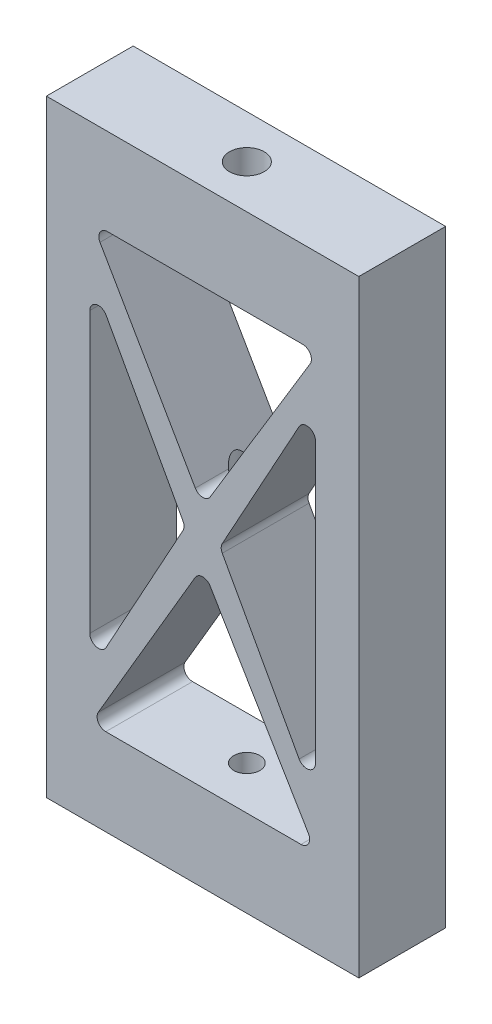
SolidWorks part; units mm, degrees
ref_plane "Ebene vorne" through (0, 0, 0) normal (0, 0, 1) x (1, 0, 0)
ref_plane "Ebene oben" through (0, 0, 0) normal (0, 1, 0) x (1, 0, 0)
ref_plane "Ebene rechts" through (0, 0, 0) normal (1, 0, 0) x (0, 0, -1)
sketch "Skizze1" plane through (0, 0, 0) normal (0, 0, 1) x (1, 0, 0)
  line L0 (-13.0958, 70) -> (22.9042, 70)
  line L5 (-13.0958, 0) -> (22.9042, 0)
  line L6 (-13.0958, 70) -> (-13.0958, 0)
  line L7 (22.9042, 70) -> (22.9042, 0)
  line L10 (17.9042, 51.1068) -> (17.9042, 18.8932)
  line L11 (-8.0958, 51.1068) -> (-8.0958, 18.8932)
  line L12 (16.028, 51.5887) -> (7.1693, 35.4819)
  line L13 (7.1693, 34.5181) -> (16.028, 18.4113)
  line L14 (-6.2196, 51.5887) -> (2.6392, 35.4819)
  line L15 (2.6392, 34.5181) -> (-6.2196, 18.4113)
  line L16 (-6.0537, 60) -> (16.4413, 60)
  line L17 (17.2969, 58.4823) -> (5.7804, 39.4481)
  line L18 (4.0586, 39.4662) -> (-6.9199, 58.5004)
  line L19 (-6.2541, 10) -> (16.241, 10)
  line L20 (17.1003, 11.5115) -> (5.7699, 30.5458)
  line L21 (4.048, 30.5403) -> (-7.1167, 11.5059)
  arc A0 (17.9042, 51.1068) -> (16.028, 51.5887) centre (16.9042, 51.1068) ccw
  arc A1 (17.9042, 18.8932) -> (16.028, 18.4113) centre (16.9042, 18.8932) cw
  arc A2 (7.1693, 35.4819) -> (7.1693, 34.5181) centre (8.0455, 35) ccw
  arc A3 (5.7804, 39.4481) -> (4.0586, 39.4662) centre (4.9248, 39.9658) cw
  arc A4 (16.4413, 60) -> (17.2969, 58.4823) centre (16.4413, 59) cw
  arc A5 (-6.0537, 60) -> (-6.9199, 58.5004) centre (-6.0537, 59) ccw
  arc A6 (-8.0958, 51.1068) -> (-6.2196, 51.5887) centre (-7.0958, 51.1068) cw
  arc A7 (-8.0958, 18.8932) -> (-6.2196, 18.4113) centre (-7.0958, 18.8932) ccw
  arc A8 (2.6392, 35.4819) -> (2.6392, 34.5181) centre (1.763, 35) cw
  arc A9 (5.7699, 30.5458) -> (4.048, 30.5403) centre (4.9106, 30.0343) ccw
  arc A10 (16.241, 10) -> (17.1003, 11.5115) centre (16.241, 11) ccw
  arc A11 (-6.2541, 10) -> (-7.1167, 11.5059) centre (-6.2541, 11) cw
  point P8 (4.9042, 41.6476)
  point P18 (17.9042, 55)
  point P22 (17.9042, 15)
  point P25 (6.9042, 35)
  point P28 (4.9042, 38)
  point P35 (-8.0958, 55)
  point P38 (-8.0958, 15)
  point P41 (2.9042, 35)
  point P44 (4.9042, 32)
  dimension "D7" = 11
  dimension "D8" = 11
  dimension "D9" = 18
  dimension "D10" = 10
  dimension "D17" = 1
  dimension "D1" = 5
  dimension "D2" = 40
  dimension "D3" = 40
  dimension "D4" = 70
  dimension "D5" = 36
  dimension "D6" = 5
  dimension "D11" = 10
  dimension "D12" = 18
  dimension "D13" = 35
  dimension "D14" = 35
  dimension "D15" = 32
  dimension "D16" = 32
extrude "Aufsatz-Linear austragen1" add sketch "Skizze1" along normal blind 10
sketch "Skizze2" plane through (0, 70, 0) normal (0, 1, 0) x (1, 0, 0)
  circle A0 centre (5, -5) radius 1.5
  dimension "D1" = 3
extrude "Schnitt-Linear austragen1" cut sketch "Skizze2" against normal through all
sketch "Skizze3" plane through (0, 70, 0) normal (0, 1, 0) x (1, 0, 0)
  circle A0 centre (5, -5) radius 2
  dimension "D1" = 4
extrude "Schnitt-Linear austragen2" cut sketch "Skizze3" against normal blind 6
sketch "Skizze4" plane through (0, 0, 0) normal (0, -1, 0) x (1, 0, 0)
  circle A0 centre (5, 5) radius 2
  dimension "D1" = 4
extrude "Schnitt-Linear austragen3" cut sketch "Skizze4" against normal blind 6
